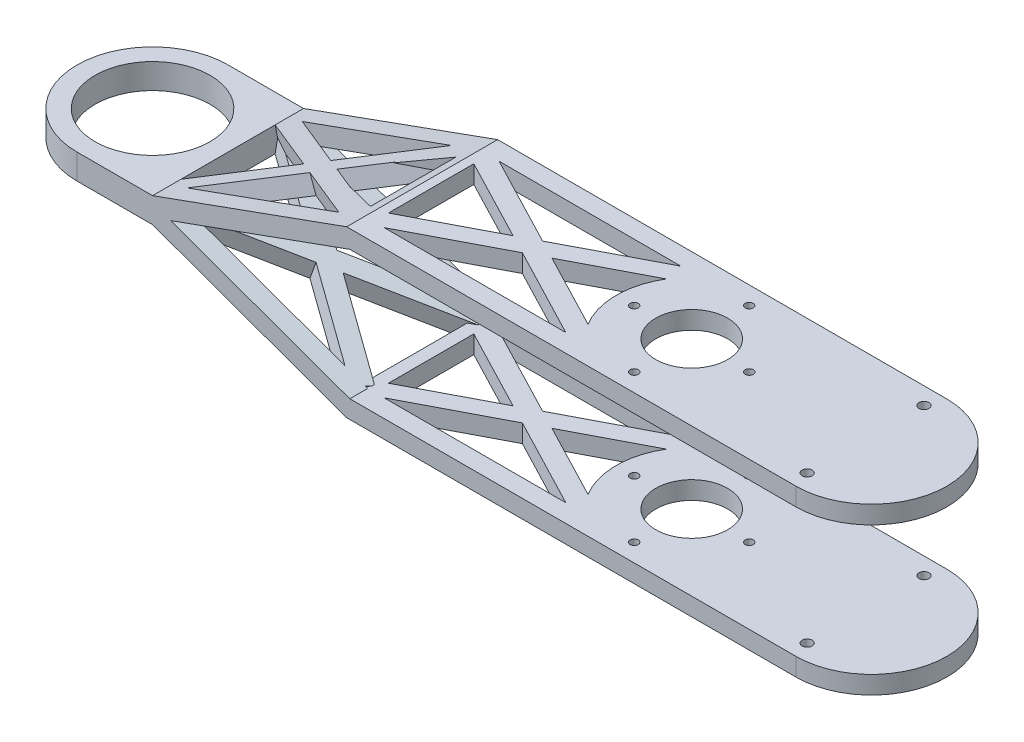
SolidWorks part; units mm, degrees
ref_plane "정면" through (0, 0, 0) normal (0, 0, 1) x (1, 0, 0)
ref_plane "윗면" through (0, 0, 0) normal (0, 1, 0) x (1, 0, 0)
ref_plane "우측면" through (0, 0, 0) normal (1, 0, 0) x (0, 0, -1)
sketch "스케치1" plane through (0, 0, 0) normal (0, 1, 0) x (1, 0, 0)
  line L0 (68.9106, 15.7059) -> (118.9106, 15.7059)
  line L2 (118.9106, -26.2941) -> (68.9106, -26.2941)
  arc A0 (68.9106, 15.7059) -> (68.9106, -26.2941) centre (68.9106, -5.2941) ccw
  circle A1 centre (-81.0894, -5.2941) radius 21
  circle A2 centre (-81.0894, -5.2941) radius 16
  circle A3 centre (68.9106, -5.2941) radius 10
  arc A4 (118.9106, -26.2941) -> (118.9106, 15.7059) centre (118.9106, -5.2941) ccw
  dimension "D1" = 42
  dimension "D2" = 42
  dimension "D5" = 32
  dimension "D6" = 20
  dimension "D3" = 150
  dimension "D4" = 0
  dimension "D7" = 50
extrude "보스-돌출1" add sketch "스케치1" along normal blind 46
sketch "스케치2" plane through (0, 46, 0) normal (0, 1, 0) x (1, 0, 0)
  line L0 (-81.0894, -26.2941) -> (68.9106, -26.2941)
  line L1 (-81.0894, 15.7059) -> (68.9106, 15.7059)
  line L2 (-81.0894, -21.2941) -> (68.9106, -21.2941)
  line L3 (-81.0894, 10.7059) -> (68.9106, 10.7059)
  line L4 (-81.0894, -26.2941) -> (-81.0894, -21.2941)
  line L5 (68.9106, -26.2941) -> (68.9106, -21.2941)
  line L6 (68.9106, 10.7059) -> (68.9106, 15.7059)
  line L7 (-81.0894, 10.7059) -> (-81.0894, 15.7059)
  circle A0 centre (-81.0894, -5.2941) radius 21 construction
  circle A3 centre (68.9106, -5.2941) radius 21 construction
  circle A4 centre (-81.0894, -5.2941) radius 16 construction
  dimension "D1" = 150
  dimension "D2" = 5
  dimension "D3" = 150
extrude "보스-돌출3" add sketch "스케치2" against normal blind 5
sketch "스케치3" plane through (0, 0, 0) normal (0, -1, 0) x (1, 0, 0)
  line L0 (68.9106, -15.7059) -> (-81.0894, -15.7059)
  line L1 (68.9106, 26.2941) -> (-81.0894, 26.2941)
  line L2 (68.9106, 26.2941) -> (68.9106, 21.2941)
  line L3 (68.9106, -10.7059) -> (68.9106, -15.7059)
  line L4 (68.9106, 21.2941) -> (-81.0894, 21.2941)
  line L6 (-81.0894, -10.7059) -> (68.9106, -10.7059)
  line L7 (-81.0894, 26.2941) -> (-81.0894, 21.2941)
  line L8 (-81.0894, -10.7059) -> (-81.0894, -15.7059)
  circle A0 centre (68.9106, 5.2941) radius 21 construction
  circle A1 centre (-81.0894, 5.2941) radius 21 construction
  circle A3 centre (-81.0894, 5.2941) radius 16 construction
extrude "보스-돌출4" add sketch "스케치3" against normal blind 5
sketch "스케치4" plane through (0, 0, 0) normal (0, -1, 0) x (1, 0, 0)
  line L0 (-6.0894, 21.2941) -> (-6.0894, -10.7059) construction
  line L1 (-67.488, 21.2941) -> (55.3091, 21.2941) construction
  line L2 (55.3091, -10.7059) -> (-67.488, -10.7059) construction
  line L3 (-6.0894, -10.7059) -> (55.3091, 21.2941) construction
  line L4 (-36.7887, 8.1132) -> (-7.2449, 23.511)
  line L5 (55.3091, -10.7059) -> (-6.0894, 21.2941) construction
  line L6 (-67.488, -10.7059) -> (-6.0894, 21.2941) construction
  line L7 (-67.488, 21.2941) -> (-6.0894, -10.7059) construction
  line L8 (-6.0894, 21.2941) -> (-7.2449, 23.511)
  line L9 (-4.934, -12.9229) -> (24.6098, 2.4749)
  line L10 (56.4646, -8.489) -> (30.019, 5.2941)
  line L11 (-66.3325, -12.9229) -> (-36.7887, 2.4749)
  line L12 (-68.6434, 19.0771) -> (-42.1978, 5.2941)
  line L13 (-31.3795, 5.2941) -> (-8.5894, -6.5838)
  line L14 (54.1537, -12.9229) -> (24.6098, 2.4749)
  line L15 (-68.6434, -8.489) -> (-42.1978, 5.2941)
  line L16 (-66.3325, 23.511) -> (-36.7887, 8.1132)
  line L17 (-68.6434, 19.0771) -> (-66.3325, 23.511)
  line L18 (-68.6434, -8.489) -> (-66.3325, -12.9229)
  line L19 (-36.7887, 2.4749) -> (-7.2449, -12.9229)
  line L20 (-6.0894, 21.2941) -> (-4.934, 23.511)
  line L21 (-68.6434, -8.489) -> (-7.2449, 23.511) construction
  line L22 (54.1537, -12.9229) -> (56.4646, -8.489)
  line L23 (-7.2449, -12.9229) -> (-4.934, -12.9229)
  line L24 (54.1537, 23.511) -> (56.4646, 19.0771)
  line L26 (-3.5894, -6.5838) -> (19.2007, 5.2941)
  line L27 (-66.3325, 23.511) -> (-4.934, -8.489) construction
  line L32 (24.6098, 8.1132) -> (54.1537, 23.511)
  line L33 (-31.3795, 5.2941) -> (-8.5894, 17.1719)
  line L34 (19.2007, 5.2941) -> (-3.5894, 17.1719)
  line L35 (30.019, 5.2941) -> (56.4646, 19.0771)
  line L36 (54.1537, -12.9229) -> (-7.2449, 19.0771) construction
  line L37 (24.6098, 8.1132) -> (-4.934, 23.511)
  line L38 (-4.934, -12.9229) -> (56.4646, 19.0771) construction
  line L39 (-8.5894, 17.1719) -> (-8.5894, -6.5838)
  line L40 (56.4646, -8.489) -> (-4.934, 23.511) construction
  line L41 (-68.6434, 19.0771) -> (-7.2449, -12.9229) construction
  line L42 (-66.3325, -12.9229) -> (-4.934, 19.0771) construction
  line L43 (-3.5894, 17.1719) -> (-3.5894, -6.5838)
  arc A0 (-67.488, -10.7059) -> (-67.488, 21.2941) centre (-81.0894, 5.2941) ccw construction
  point P15 (-6.0894, 5.2941)
  point P17 (-8.5894, 21.2941)
  point P18 (-8.5894, -10.7059)
  point P19 (-3.5894, 21.2941)
  point P20 (-3.5894, -10.7059)
  point P29 (-7.2449, -8.489)
  dimension "D3" = 2.5
  dimension "D4" = 2.5
extrude "보스-돌출5" add sketch "스케치4" against normal blind 5
sketch "스케치6" plane through (0, 0, -15.7059) normal (0, 0, -1) x (-1, 0, 0)
  line L0 (-68.9106, 41) -> (81.0894, 41) construction
  line L1 (9.3515, 5) -> (-160.0584, 5)
  line L2 (9.3515, 5) -> (9.3515, 41)
  line L3 (9.3515, 41) -> (-160.0584, 41)
  line L4 (-160.0584, 5) -> (-160.0584, 41)
  line L5 (9.3515, 5) -> (-160.0584, 41) construction
  line L6 (9.3515, 41) -> (-160.0584, 5) construction
  line L7 (81.0894, 5) -> (-68.9106, 5) construction
  point P0 (-75.3535, 23)
  dimension "D1" = 0
  dimension "D2" = 0
extrude "컷-돌출1" cut sketch "스케치6" against normal up to surface (42 mm away) up to face at (6.4106, 23, 26.2941)
ref_plane "평면1" through (0, 23, 0) normal (0, 1, 0) x (1, 0, 0)
mirror "대칭 복사1" about plane through (0, 23, 0) normal (0, 1, 0) of "보스-돌출5"
sketch "스케치7" plane through (0, 0, -15.7059) normal (0, 0, -1) x (-1, 0, 0)
  line L0 (6.0894, 0) -> (60.0894, 19.5)
  line L1 (-118.9106, 0) -> (81.0894, 0) construction
  line L2 (81.0894, 41) -> (81.0894, 5) construction
  line L3 (102.0894, 62.4765) -> (102.0894, -18.1587) construction
  line L6 (108.0894, 19.5) -> (108.0894, 26.5)
  line L7 (60.0894, 19.5) -> (108.0894, 19.5)
  line L9 (6.0894, 46) -> (127.8141, 46)
  line L10 (127.8141, 46) -> (127.8141, 0)
  line L11 (127.8141, 0) -> (6.0894, 0)
  line L12 (23.1, 23) -> (-23.1, 23) construction
  line L13 (60.0894, 46) -> (60.0894, 0) construction
  line L15 (108.0894, 26.5) -> (60.0894, 26.5)
  line L16 (60.0894, 46) -> (60.0894, 0) construction
  line L17 (60.0894, 26.5) -> (6.0894, 46)
  line L20 (6.0894, 49.3069) -> (6.0894, -6.2164) construction
  line L21 (-118.9106, 46) -> (81.0894, 46) construction
  point P1 (108.0894, 23)
  dimension "D1" = 121.7247
  dimension "D2" = 7
  dimension "D3" = 0
  dimension "D4" = 48
  dimension "D5" = 21
  dimension "D6" = 75
extrude "컷-돌출4" cut sketch "스케치7" against normal up to surface (42 mm away) up to face at (18.9106, 43.5, 26.2941)
sketch "스케치9" plane through (0, 0, -15.7059) normal (0, 0, -1) x (-1, 0, 0)
  line L0 (4.3912, 41.2972) -> (55.0605, 23)
  line L1 (55.0605, 23) -> (4.3912, 4.7028)
  line L2 (4.3912, 41.2972) -> (6.0894, 46)
  line L3 (88.5238, 35.084) -> (4.3912, 4.7028) construction
  line L4 (69.7817, 23) -> (6.0894, 0)
  line L5 (6.0894, 46) -> (69.7817, 23)
  line L6 (90.222, 30.3812) -> (6.0894, 0) construction
  line L7 (6.0894, 46) -> (82.6926, 18.3377) construction
  line L8 (4.3912, 41.2972) -> (80.9944, 13.635) construction
  line L9 (6.0894, 0) -> (4.3912, 4.7028)
  dimension "D1" = 5
extrude "보스-돌출7" add sketch "스케치9" against normal blind 5
sketch "스케치10" plane through (0, 0, -15.7059) normal (0, 0, -1) x (-1, 0, 0)
  line L0 (60.0894, 26.5) -> (60.0894, 19.5)
  line L1 (69.7817, 23) -> (6.0894, 46) construction
  line L2 (69.7817, 23) -> (6.0894, 0) construction
  line L3 (60.0894, 19.5) -> (81.0894, 19.5)
  line L4 (81.0894, 19.5) -> (81.0894, 26.5)
  line L5 (81.0894, 26.5) -> (60.0894, 26.5)
  dimension "D1" = 7
  dimension "D2" = 21
extrude "보스-돌출8" add sketch "스케치10" against normal up to surface up to face at (-68.2333, 23, -11.2972)
ref_plane "평면2" through (0, 0, 5.2941) normal (0, 0, -1) x (-1, 0, 0)
mirror "대칭 복사2" about plane through (0, 0, 5.2941) normal (0, 0, -1) of "보스-돌출8", "보스-돌출7"
sketch "스케치11" plane through (-0.7025, -1.9453, 0) normal (-0.3396, -0.9406, 0) x (0.9406, -0.3396, 0)
  line L1 (-63.1404, 21.2941) -> (-8.3904, 21.2941)
  line L2 (-63.1404, 21.2941) -> (-63.1404, -11.161)
  line L3 (-63.1404, -11.161) -> (-8.3904, -11.161)
  line L4 (-8.3904, 21.2941) -> (-8.3904, -11.161)
  dimension "D1" = 54.75
extrude "컷-돌출5" cut sketch "스케치11" against normal blind 5
sketch "스케치12" plane through (-0.7025, -1.9453, 0) normal (-0.3396, -0.9406, 0) x (0.9406, -0.3396, 0)
  line L0 (-31.0303, 5.1659) -> (-6.2462, -9.5258)
  line L1 (-64.1838, -14.2115) -> (-35.9676, 2.2802)
  line L2 (-35.9497, 8.082) -> (-8.8411, 23.9263)
  line L3 (-66.4731, 20.3634) -> (-40.887, 5.1963)
  line L4 (-66.7068, -9.8947) -> (-40.887, 5.1963)
  line L5 (-63.9235, 24.6645) -> (-35.9497, 8.082)
  line L6 (-35.9676, 2.2802) -> (-8.7958, -13.8269)
  line L7 (-31.0303, 5.1659) -> (-6.3181, 19.6096)
  line L8 (-66.4731, 20.3634) -> (-63.9235, 24.6645)
  line L9 (-8.8411, 23.9263) -> (-6.3181, 19.6096)
  line L11 (-6.2462, -9.5258) -> (-8.7958, -13.8269)
  line L12 (-66.7068, -9.8947) -> (-64.1838, -14.2115)
extrude "보스-돌출15" add sketch "스케치12" against normal blind 5
mirror "대칭 복사3" about plane through (0, 23, 0) normal (0, 1, 0) of "보스-돌출15"
sketch "스케치13" plane through (0, 46, 0) normal (0, 1, 0) x (1, 0, 0)
  line L1 (68.9106, -5.2941) -> (52.9106, -5.2941) construction
  line L2 (52.9106, -5.2941) -> (84.9106, -5.2941) construction
  line L3 (84.9106, -5.2941) -> (68.9106, -21.2941) construction
  line L4 (68.9106, -21.2941) -> (68.9106, 10.7059) construction
  circle A0 centre (68.9106, -5.2941) radius 16 construction
  circle A1 centre (84.9106, -5.2941) radius 1.125
  circle A2 centre (52.9106, -5.2941) radius 1.125
  circle A3 centre (68.9106, -21.2941) radius 1.125
  circle A4 centre (68.9106, 10.7059) radius 1.125
  dimension "D1" = 2.25
  dimension "D2" = 2.25
  dimension "D3" = 2.25
  dimension "D4" = 2.25
  dimension "D5" = 32
extrude "컷-돌출6" cut sketch "스케치13" against normal through all both and the other way through all
sketch "스케치14" plane through (0, 46, 0) normal (0, 1, 0) x (1, 0, 0)
  line L0 (118.9106, 15.7059) -> (-6.0894, 15.7059) construction
  line L5 (-6.0894, -26.2941) -> (118.9106, -26.2941) construction
  circle A0 centre (117.2772, 10.9559) radius 1.4
  circle A1 centre (117.2772, -21.5441) radius 1.4
  dimension "D1" = 2.8
  dimension "D2" = 2.8
  dimension "D3" = 32.5
  dimension "D4" = 42
  dimension "D5" = 4.75
extrude "컷-돌출7" cut sketch "스케치14" against normal through all both and the other way through all
